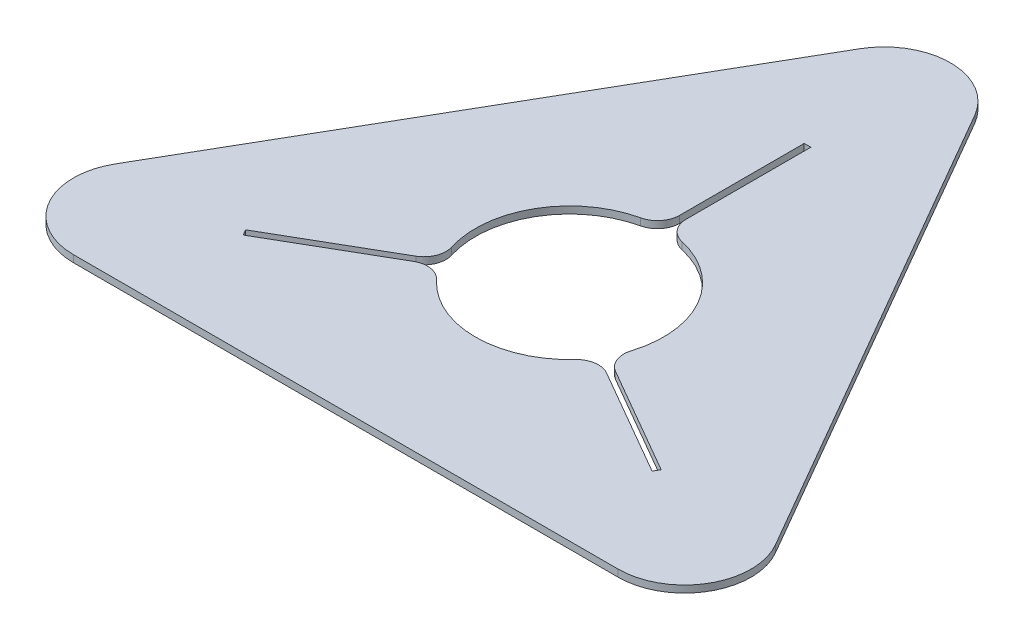
SolidWorks part; units mm, degrees
material "Beech"
ref_plane "Front Plane" through (0, 0, 0) normal (0, 0, 1) x (1, 0, 0)
ref_plane "Top Plane" through (0, 0, 0) normal (0, 1, 0) x (1, 0, 0)
ref_plane "Right Plane" through (0, 0, 0) normal (1, 0, 0) x (0, 0, -1)
sketch "Sketch1" plane through (0, 0, 0) normal (0, 1, 0) x (1, 0, 0)
  line L0 (0, 0) -> (-350, -606.2178)
  line L1 (-350, -606.2178) -> (350, -606.2178)
  line L2 (350, -606.2178) -> (0, 0)
extrude "Boss-Extrude1" add sketch "Sketch1" along normal blind 6.35
sketch "Sketch2" plane through (0, 6.35, 0) normal (0, 1, 0) x (1, 0, 0)
  circle A0 centre (0, -404.1452) radius 85
  dimension "D1" = 170
extrude "Cut-Extrude1" cut sketch "Sketch2" against normal blind 6.35
fillet "Fillet1" radius 60 3 edges at (0, 3.175, 0) (350, 3.175, 606.2178) (-350, 3.175, 606.2178)
sketch "Sketch3" plane through (0, 6.35, 0) normal (0, 1, 0) x (1, 0, 0)
  line L0 (27.4808, -416.5471) -> (24.4808, -421.7433)
  line L1 (-3, -374.1452) -> (3, -374.1452)
  line L2 (-3, -374.1452) -> (-3, -189.1452)
  line L3 (-3, -189.1452) -> (3, -189.1452)
  line L4 (3, -374.1452) -> (3, -189.1452)
  line L5 (27.4808, -416.5471) -> (187.6955, -509.0471)
  line L6 (187.6955, -509.0471) -> (184.6955, -514.2433)
  line L7 (24.4808, -421.7433) -> (184.6955, -514.2433)
  line L8 (-24.4808, -421.7433) -> (-27.4808, -416.5471)
  line L9 (-24.4808, -421.7433) -> (-184.6955, -514.2433)
  line L10 (-184.6955, -514.2433) -> (-187.6955, -509.0471)
  line L11 (-27.4808, -416.5471) -> (-187.6955, -509.0471)
  circle A0 centre (0, -404.1452) radius 85 construction
  point P4 (0, -374.1452)
  point P18 (0, -404.1452)
  dimension "D1" = 0
  dimension "D2" = 30
  dimension "D3" = 185
  dimension "D4" = 6
  dimension "D5" = 3
extrude "Cut-Extrude2" cut sketch "Sketch3" against normal blind 6.35
fillet "Fillet2" radius 20 6 edges at (-3, 3.175, 319.1981) (3, 3.175, 319.1981) (75.0663, 3.175, 444.0206) (72.0663, 3.175, 449.2168) (-72.0663, 3.175, 449.2168) (-75.0663, 3.175, 444.0206)
